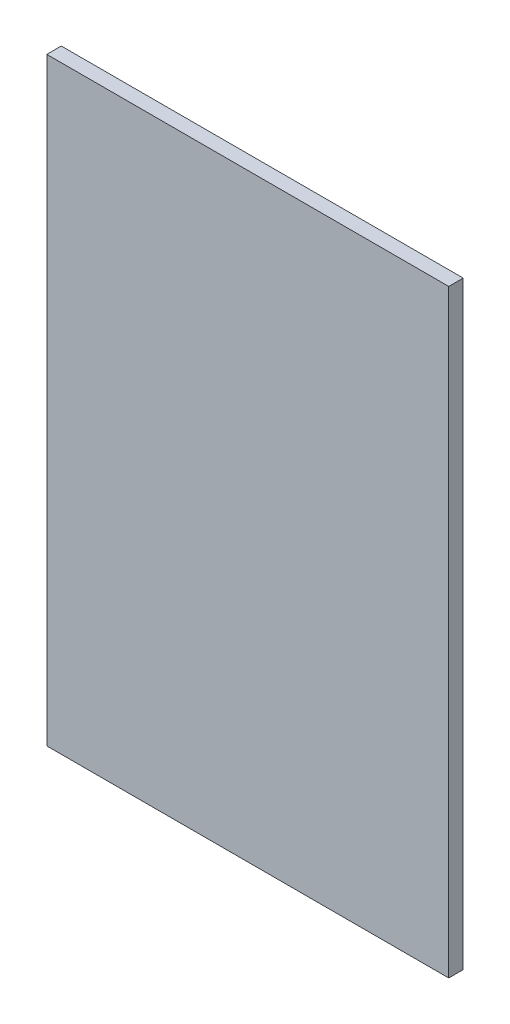
SolidWorks part; units mm, degrees
ref_plane "Front Plane" through (0, 0, 0) normal (0, 0, 1) x (1, 0, 0)
ref_plane "Top Plane" through (0, 0, 0) normal (0, 1, 0) x (1, 0, 0)
ref_plane "Right Plane" through (0, 0, 0) normal (1, 0, 0) x (0, 0, -1)
sketch "Sketch1" plane through (0, 0, 0) normal (0, 0, 1) x (1, 0, 0)
  line L1 (250, -372.5) -> (-250, -372.5)
  line L2 (250, -372.5) -> (250, 372.5)
  line L3 (250, 372.5) -> (-250, 372.5)
  line L4 (-250, -372.5) -> (-250, 372.5)
  line L5 (250, -372.5) -> (-250, 372.5) construction
  line L6 (250, 372.5) -> (-250, -372.5) construction
  point P0 (0, 0)
  dimension "D1" = 745
  dimension "D2" = 500
extrude "Boss-Extrude1" add sketch "Sketch1" along normal blind 18
equation "\"H_DSP\"=10"
